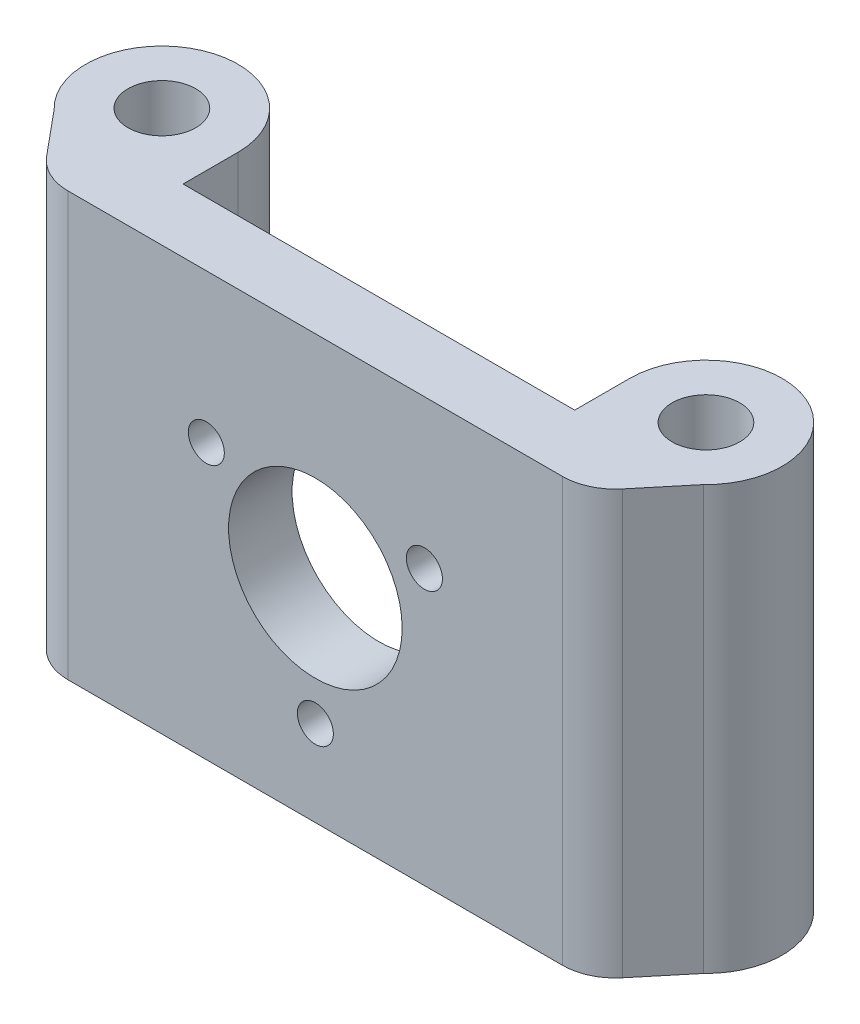
SolidWorks part; units mm, degrees
ref_plane "Front Plane" through (0, 0, 0) normal (0, 0, 1) x (1, 0, 0)
ref_plane "Top Plane" through (0, 0, 0) normal (0, 1, 0) x (1, 0, 0)
ref_plane "Right Plane" through (0, 0, 0) normal (1, 0, 0) x (0, 0, -1)
sketch "Sketch1" plane through (0, 0, 0) normal (0, 1, 0) x (1, 0, 0)
  line L0 (-18.5, 0) -> (18.5, 0)
  line L1 (18.5, 0) -> (18.5, 6)
  line L4 (18.5, 6) -> (-18.5, 6)
  line L7 (-18.5, 6) -> (-18.5, 0)
  line L8 (0, -667.3852) -> (0, 32701.8756) construction
  line L9 (18.5, 6) -> (18.5, 11.2)
  line L10 (18.5, 0) -> (25.7, 0)
  line L11 (25.7, 0) -> (30.68, 6)
  line L12 (-18.5, 6) -> (-18.5, 11.2)
  line L13 (-25.7, 0) -> (-30.68, 6)
  line L14 (-18.5, 0) -> (-25.7, 0)
  circle A0 centre (25.7, 11.2) radius 3.2
  arc A1 (30.68, 6) -> (18.5, 11.2) centre (25.7, 11.2) ccw
  circle A2 centre (25.7, 11.2) radius 7.2 construction
  circle A3 centre (-25.7, 11.2) radius 3.2
  arc A4 (-30.68, 6) -> (-18.5, 11.2) centre (-25.7, 11.2) cw
  dimension "D3" = 6.4
  dimension "D5" = 4
  dimension "D1" = 6
  dimension "D2" = 37
  dimension "D4" = 4
extrude "Boss-Extrude1" add sketch "Sketch1" along normal mid plane 40
sketch "Sketch2" plane through (0, 0, 0) normal (0, 0, 1) x (1, 0, 0)
  line L0 (10.3, 5.9467) -> (0, -11.8934) construction
  line L1 (0, -11.8934) -> (-10.3, 5.9467) construction
  line L2 (-10.3, 5.9467) -> (10.3, 5.9467) construction
  circle A0 centre (0, 0) radius 8.2
  circle A1 centre (0, 0) radius 5.9467 construction
  circle A2 centre (0, -11.8934) radius 1.7
  circle A3 centre (-10.3, 5.9467) radius 1.7
  circle A4 centre (10.3, 5.9467) radius 1.7
  dimension "D1" = 16.4
  dimension "D3" = 3.4
  dimension "D2" = 20.6
extrude "Cut-Extrude2" cut sketch "Sketch2" along normal through all from surface at -6 starting at face at (0, 0, -6)
fillet "Fillet1" radius 5 2 edges at (25.7, 0, 0) (-25.7, 0, 0)
